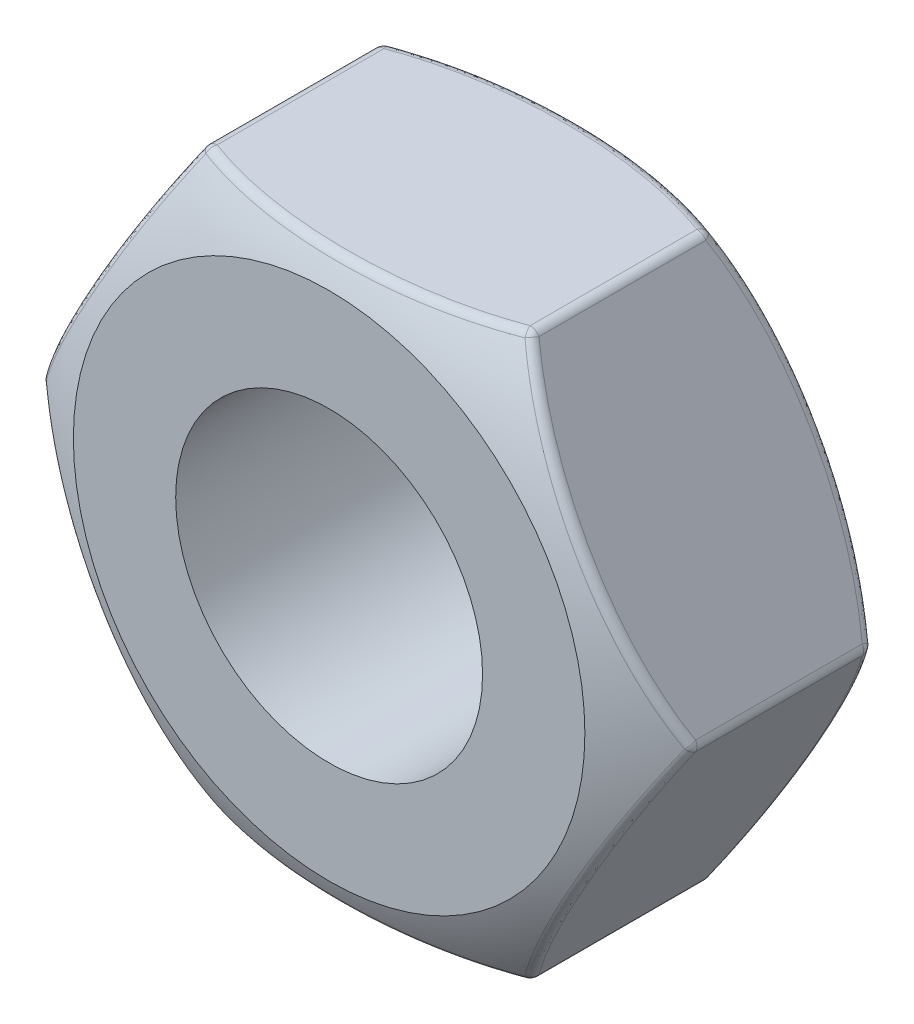
SolidWorks part; units mm, degrees
ref_plane "Front Plane" through (0, 0, 0) normal (0, 0, 1) x (1, 0, 0)
ref_plane "Top Plane" through (0, 0, 0) normal (0, 1, 0) x (1, 0, 0)
ref_plane "Right Plane" through (0, 0, 0) normal (1, 0, 0) x (0, 0, -1)
sketch "Sketch1" plane through (0, 0, 0) normal (0, 0, 1) x (1, 0, 0)
  line L1 (3.1754, 0) -> (1.5877, 2.75)
  line L2 (1.5877, 2.75) -> (-1.5877, 2.75)
  line L3 (-1.5877, 2.75) -> (-3.1754, 0)
  line L4 (-3.1754, 0) -> (-1.5877, -2.75)
  line L5 (-1.5877, -2.75) -> (1.5877, -2.75)
  line L6 (1.5877, -2.75) -> (3.1754, 0)
  circle A0 centre (0, 0) radius 2.75 construction
  dimension "D1" = 5.5
extrude "Extrude1" add sketch "Sketch1" along normal blind 2.5
sketch "Sketch2" plane through (0, 0, 0) normal (1, 0, 0) x (0, 0, -1)
  line L0 (1.0118, 0) -> (-3.858, 0) construction
  line L1 (0, 2.75) -> (0, 0) construction
  line L3 (-0.5, 3.3) -> (0.4733, 3.3)
  line L4 (0.4733, 3.3) -> (0.4733, 2.5)
  line L5 (0.4733, 2.5) -> (0, 2.5)
  line L6 (-2.5, 2.75) -> (-2.5, 0) construction
  line L7 (-2, 3.3) -> (-2.8363, 3.3)
  line L8 (-2.8363, 3.3) -> (-2.8363, 2.5)
  line L9 (-2.8363, 2.5) -> (-2.5, 2.5)
  arc A0 (0, 2.5) -> (-0.5, 3.3) centre (-2.7624, 1.3298) ccw
  arc A1 (-2, 3.3) -> (-2.5, 2.5) centre (0.2624, 1.3298) ccw
  dimension "D4" = 3
  dimension "D5" = 3.3
  dimension "D8" = 3
  dimension "D1" = 2.5
  dimension "D2" = 3.3
  dimension "D3" = 0.5
  dimension "D6" = 2.5
  dimension "D7" = 0.5
revolve "Cut-Revolve1" cut sketch "Sketch2" angle 360 about L0
sketch "Sketch3" plane through (0, 0, 2.5) normal (0, 0, 1) x (1, 0, 0)
  circle A0 centre (0, 0) radius 1.5
  dimension "D1" = 3
extrude "Cut-Extrude1" cut sketch "Sketch3" against normal blind 12.5
fillet "Fillet1" radius 0.1 6 edges at (-1.5877, 2.75, 1.25) (-3.1754, 0, 1.25) (-1.5877, -2.75, 1.25) (1.5877, -2.75, 1.25) (3.1754, 0, 1.25) (1.5877, 2.75, 1.25)
fillet "Fillet2" radius 0.1 24 edges at (-3.1598, 0.0047, 0.3852) (-2.2431, 1.6149, 0.1273) (-1.5759, 2.7388, 0.3852) (-0.6098, 2.75, 5.3679) (1.584, 2.7342, 0.3852) (2.5201, 1.1351, 0.1273) (3.1598, -0.0047, 0.3852) (2.2431, -1.6149, 0.1273) (1.5759, -2.7388, 0.3852) (0.6098, -2.75, 5.3679) (-1.584, -2.7342, 0.3852) (-1.5759, -2.7388, 2.1148) (-0.6098, -2.75, -2.8679) (1.584, -2.7342, 2.1148) (2.5201, -1.1351, 2.3727) (3.1598, 0.0047, 2.1148) (2.2431, 1.6149, 2.3727) (1.5759, 2.7388, 2.1148) (0.6098, 2.75, -2.8679) (-1.584, 2.7342, 2.1148) (-2.5201, 1.1351, 2.3727) (-3.1598, -0.0047, 2.1148) (-2.5201, -1.1351, 0.1273) (-2.2431, -1.6149, 2.3727)
